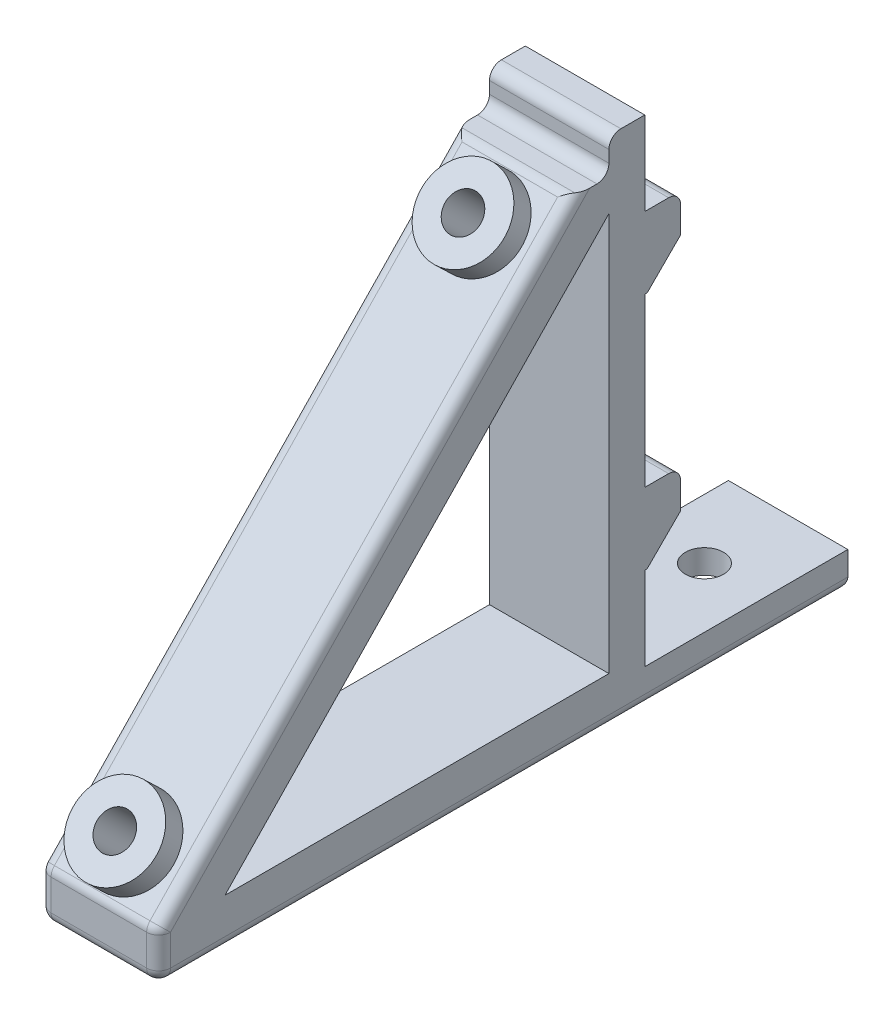
SolidWorks part; units mm, degrees
ref_plane "Front Plane" through (0, 0, 0) normal (0, 0, 1) x (1, 0, 0)
ref_plane "Top Plane" through (0, 0, 0) normal (0, 1, 0) x (1, 0, 0)
ref_plane "Right Plane" through (0, 0, 0) normal (1, 0, 0) x (0, 0, -1)
sketch "Sketch1" plane through (0, 0, 0) normal (0, 1, 0) x (1, 0, 0)
  line L1 (5, -10) -> (-5, -10)
  line L2 (5, -10) -> (5, 10)
  line L3 (5, 10) -> (-5, 10)
  line L4 (-5, -10) -> (-5, 10)
  line L5 (5, -10) -> (-5, 10) construction
  line L6 (5, 10) -> (-5, -10) construction
  point P0 (0, 0)
  dimension "D1" = 10
  dimension "D2" = 20
extrude "Boss-Extrude1" add sketch "Sketch1" along normal blind 3
sketch "Sketch2" plane through (0, 0, 0) normal (0, -1, 0) x (1, 0, 0)
  circle A0 centre (0, 0) radius 1.6
  dimension "D1" = 3.2
extrude "Cut-Extrude1" cut sketch "Sketch2" against normal through all
sketch "Sketch3" plane through (0, 0, 0) normal (0, -1, 0) x (1, 0, 0)
  circle A0 centre (0, 0) radius 3.1
  dimension "D1" = 6.2
extrude "Cut-Extrude2" cut sketch "Sketch3" against normal offset from surface (1 mm away) 2 up to face at (0, 3, -1.6)
sketch "Sketch4" plane through (0, 0, 10) normal (0, 0, 1) x (1, 0, 0)
  line L0 (-5, 3) -> (5, 3) construction
  line L1 (-5, 0) -> (5, 0)
  line L2 (-5, 0) -> (-5, 43)
  line L3 (-5, 43) -> (5, 43)
  line L4 (5, 0) -> (5, 43)
  line L5 (5, 3) -> (5, 0) construction
  dimension "D1" = 40
extrude "Boss-Extrude2" add sketch "Sketch4" along normal blind 3
sketch "Sketch5" plane through (0, 0, 10) normal (0, 0, -1) x (-1, 0, 0)
  line L0 (-5, 23) -> (5, 23) construction
  line L1 (-5, 3) -> (-5, 43) construction
  line L2 (5, 43) -> (5, 3) construction
  line L3 (0, 43) -> (0, 23) construction
  line L4 (-5, 43) -> (5, 43) construction
  line L5 (5, 16) -> (5, 10)
  line L6 (5, 30) -> (-5, 30)
  line L7 (5, 30) -> (5, 36)
  line L8 (5, 36) -> (-5, 36)
  line L9 (-5, 30) -> (-5, 36)
  line L10 (5, 30) -> (-5, 36) construction
  line L11 (5, 36) -> (-5, 30) construction
  line L12 (5, 16) -> (-5, 16)
  line L13 (-5, 16) -> (-5, 10)
  line L14 (5, 10) -> (-5, 10)
  point P6 (0, 23)
  point P11 (0, 33)
  dimension "D1" = 6
extrude "Boss-Extrude3" add sketch "Sketch5" along normal blind 3
chamfer "Chamfer1" distance 2.8 angle 45 2 edges at (0, 10, 7) (0, 30, 7)
sketch "Sketch6" plane through (-5, 0, 0) normal (-1, 0, 0) x (0, 0, 1)
  line L0 (13, 40) -> (16, 40)
  line L1 (45.1431, 4) -> (13, 37.3486)
  line L2 (13, 43) -> (13, 0) construction
  line L3 (16, 40) -> (50.6987, 4)
  line L4 (13, 40) -> (13, 37.3486)
  line L5 (50.6987, 4) -> (50.6987, 0)
  line L6 (50.6987, 0) -> (13, 0)
  line L8 (45.1431, 4) -> (13, 4)
  line L9 (13, 4) -> (13, 0)
  line L10 (13, 0) -> (13, 43) construction
  dimension "D1" = 50
  dimension "D2" = 4
  dimension "D3" = 3
  dimension "D4" = 3
  dimension "D5" = 46.054
  dimension "D6" = 4
extrude "Boss-Extrude4" add sketch "Sketch6" against normal up to surface (10 mm away) up to face at (5, 19.225, 7.725)
sketch "Sketch7" plane through (0, -24.3221, 77.997) normal (0, -0.694, -0.72) x (1, 0, 0)
  line L0 (0, -39.3362) -> (0, -89.3362) construction
  line L3 (-5, -64.3362) -> (5, -64.3362) construction
  line L6 (5, -89.3362) -> (-5, -89.3362) construction
  line L7 (5, -39.3362) -> (-5, -39.3362) construction
  line L8 (5, -89.3362) -> (5, -39.3362) construction
  line L9 (-5, -39.3362) -> (-5, -89.3362) construction
  circle A0 centre (0, -43.3362) radius 3.5
  circle A1 centre (0, -85.3362) radius 3.5
  dimension "D1" = 7
  dimension "D2" = 42
extrude "Boss-Extrude5" add sketch "Sketch7" against normal blind 2
sketch "Sketch10" plane through (0, 3, 0) normal (0, 1, 0) x (1, 0, 0)
  line L0 (-5, 10) -> (-5, -10) construction
  line L1 (5, 10) -> (-5, 10)
  line L2 (5, 10) -> (5, 7)
  line L3 (5, 7) -> (-5, 7)
  line L4 (-5, 10) -> (-5, 7)
  dimension "D1" = 3
extrude "Cut-Extrude6" cut sketch "Sketch10" against normal through all
fillet "Fillet2" radius 1 14 edges at (0, 43, 13) (5, 0, 21.8494) (-5, 0, 21.8494) (0, 0, -7) (0, 16, 7) (0, 36, 7) (0, 40, 13) (0, 40, 16) (5, 22, 33.3494) (-5, 22, 33.3494) (0, 4, 50.6987) (5, 2, 50.6987) (-5, 2, 50.6987) (0, 0, 50.6987)
sketch "Sketch8" plane through (0, 28.6465, 29.7209) normal (0, 0.694, 0.72) x (-1, 0, 0)
  circle A0 centre (0, 28.3036) radius 1.5
  circle A1 centre (0, -13.6964) radius 1.5
  dimension "D1" = 3
extrude "Cut-Extrude4" cut sketch "Sketch8" against normal up to surface (6 mm away) up to face at (0, 20.6743, 29.0716)
